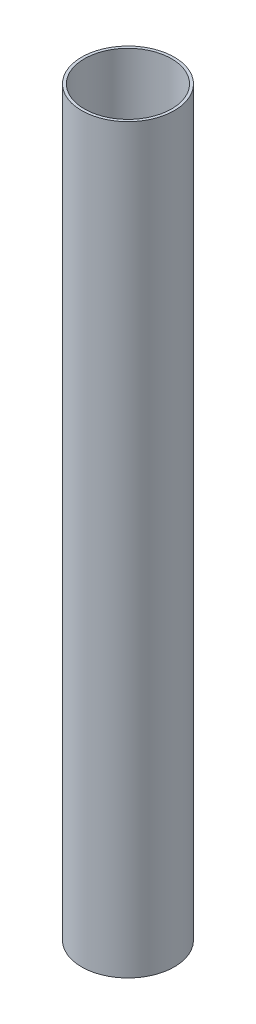
SolidWorks part; units mm, degrees
ref_plane "Front Plane" through (0, 0, 0) normal (0, 0, 1) x (1, 0, 0)
ref_plane "Top Plane" through (0, 0, 0) normal (0, 1, 0) x (1, 0, 0)
ref_plane "Right Plane" through (0, 0, 0) normal (1, 0, 0) x (0, 0, -1)
sketch "Sketch1" plane through (0, 0, 0) normal (0, 1, 0) x (1, 0, 0)
  circle A0 centre (0, 0) radius 6.35
  circle A1 centre (0, 0) radius 5.969
  dimension "D1" = 12.7
  dimension "D2" = 11.938
sketch "Sketch2" plane through (0, 0, 0) normal (1, 0, 0) x (0, 0, -1)
  line L0 (0, 0) -> (0, -101.6)
  dimension "D1" = 101.6
sweep "Sweep1" add profiles "Sketch1" path "Sketch2"
